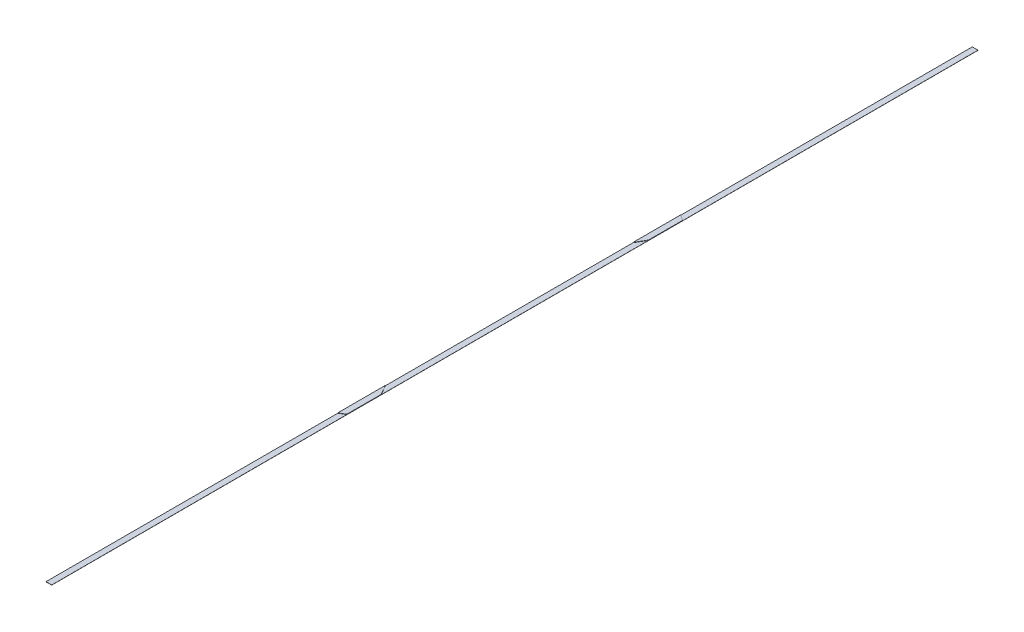
SolidWorks part; units mm, degrees
ref_plane "Front Plane" through (0, 0, 0) normal (0, 0, 1) x (1, 0, 0)
ref_plane "Top Plane" through (0, 0, 0) normal (0, 1, 0) x (1, 0, 0)
ref_plane "Right Plane" through (0, 0, 0) normal (1, 0, 0) x (0, 0, -1)
sketch "Sketch1" plane through (0, 0, 0) normal (0, 1, 0) x (1, 0, 0)
  line L1 (-25.4, 4111.9654) -> (25.4, 4111.9654)
  line L2 (-25.4, 4111.9654) -> (-25.4, -4111.9654)
  line L3 (-25.4, -4111.9654) -> (25.4, -4111.9654)
  line L4 (25.4, 4111.9654) -> (25.4, -4111.9654)
  line L5 (-25.4, 4111.9654) -> (25.4, -4111.9654) construction
  line L6 (-25.4, -4111.9654) -> (25.4, 4111.9654) construction
  point P0 (0, 0)
  dimension "D1" = 8223.9307
  dimension "D2" = 50.8
extrude "Boss-Extrude1" add sketch "Sketch1" along normal blind 1.27
sketch "Sketch3" plane through (0, 1.27, 0) normal (0, 1, 0) x (1, 0, 0)
  line L0 (-25.4, -1521.1654) -> (25.4, -1491.836)
  line L1 (-25.4, 4111.9654) -> (-25.4, -4111.9654) construction
  line L2 (25.4, -4111.9654) -> (25.4, 4111.9654) construction
  line L3 (25.4, -1491.836) -> (25.4, -1187.036)
  line L4 (25.4, -1187.036) -> (-25.4, -1099.0478)
  line L5 (-25.4, -4111.9654) -> (25.4, -4111.9654) construction
  line L6 (-25.4, 0) -> (25.4, 0) construction
  line L7 (25.4, 1187.036) -> (-25.4, 1099.0478)
  line L8 (-25.4, 1521.1654) -> (25.4, 1491.836)
  line L9 (-25.4, 1521.1654) -> (-25.4, 1099.0478)
  line L10 (25.4, -1491.836) -> (25.4, 0)
  line L11 (-25.4, 0) -> (-25.4, -1521.1654)
  line L12 (25.4, 1187.036) -> (25.4, 1491.836)
  line M4 (25.4, -4111.9654) -> (25.4, 4111.9654)
  line M6 (-25.4, 4111.9654) -> (-25.4, -4111.9654)
  dimension "D1" = 60
  dimension "D2" = 30
  dimension "D3" = 304.8
  dimension "D4" = 2590.8
extrude "Boss-Extrude2" add sketch "Sketch3" along normal blind 2.6568 contours L4 L0 M4 M6 | L9 L7 L12 L8
